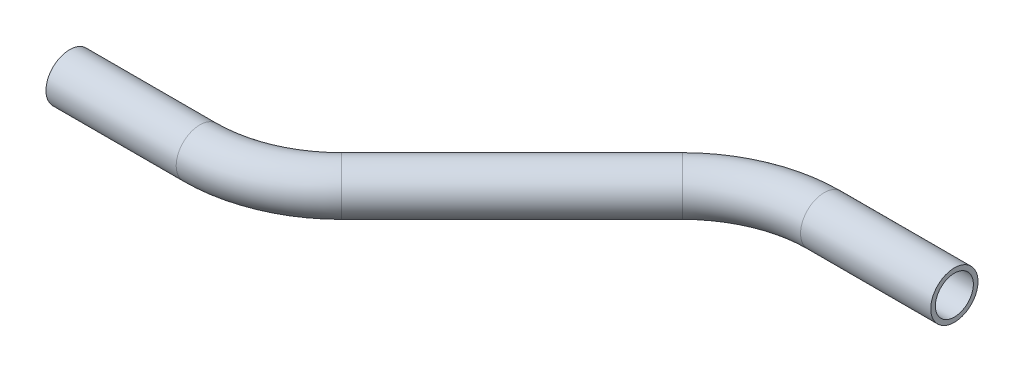
SolidWorks part; units mm, degrees
material "AISI Type 316L stainless steel"
ref_plane "Front Plane" through (0, 0, 0) normal (0, 0, 1) x (1, 0, 0)
ref_plane "Top Plane" through (0, 0, 0) normal (0, 1, 0) x (1, 0, 0)
ref_plane "Right Plane" through (0, 0, 0) normal (1, 0, 0) x (0, 0, -1)
sketch "Sketch1" plane through (0, 0, 0) normal (0, 1, 0) x (1, 0, 0)
  line L0 (0, 0) -> (35.0185, 0)
  line L1 (61.9592, 11.1592) -> (107.7969, 56.9969)
  line L2 (134.7377, 68.1561) -> (169.7561, 68.1561)
  arc A0 (107.7969, 56.9969) -> (134.7377, 68.1561) centre (134.7377, 30.0561) cw
  arc A1 (35.0185, 0) -> (61.9592, 11.1592) centre (35.0185, 38.1) ccw
  point P7 (118.9561, 68.1561)
  point P10 (50.8, 0)
  dimension "D5" = 38.1
  dimension "D1" = 50.8
  dimension "D2" = 50.8
  dimension "D3" = 135
  dimension "D4" = 68.1561
ref_plane "Plane1" through (0, 0, 0) normal (1, 0, 0) x (0, 0, -1)
sketch "Sketch2" plane through (0, 0, 0) normal (1, 0, 0) x (0, 0, -1)
  circle A0 centre (0, 0) radius 6.35
  circle A1 centre (0, 0) radius 5.1054
  dimension "D1" = 12.7
  dimension "D2" = 1.2446
sweep "Sweep1" add profiles "Sketch2" path "Sketch1"
